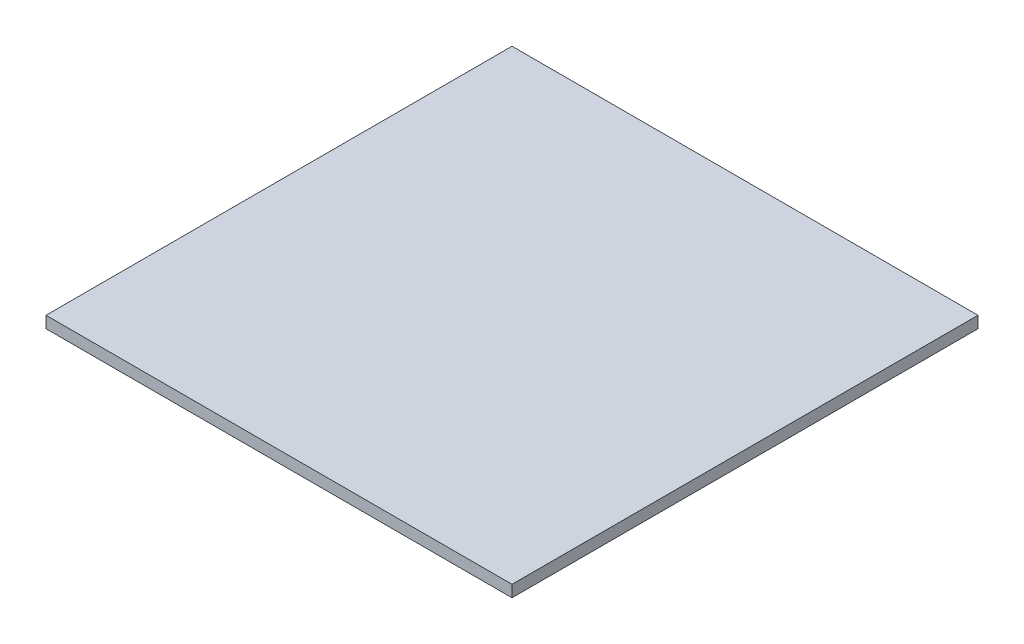
SolidWorks part; units mm, degrees
material "Cedar"
ref_plane "Front" through (0, 0, 0) normal (0, 0, 1) x (1, 0, 0)
ref_plane "Top" through (0, 0, 0) normal (0, 1, 0) x (1, 0, 0)
ref_plane "Right" through (0, 0, 0) normal (1, 0, 0) x (0, 0, -1)
sketch "Sketch1" plane through (0, 0, 0) normal (0, 1, 0) x (1, 0, 0)
  line L1 (-228.6, -228.6) -> (228.6, -228.6)
  line L2 (-228.6, -228.6) -> (-228.6, 228.6)
  line L3 (-228.6, 228.6) -> (228.6, 228.6)
  line L4 (228.6, -228.6) -> (228.6, 228.6)
  line L5 (-228.6, -228.6) -> (228.6, 228.6) construction
  line L6 (-228.6, 228.6) -> (228.6, -228.6) construction
  point P0 (0, 0)
  dimension "D1" = 457.2
  dimension "D2" = 457.2
extrude "Boss-Extrude1" add sketch "Sketch1" along normal blind 11.4554
